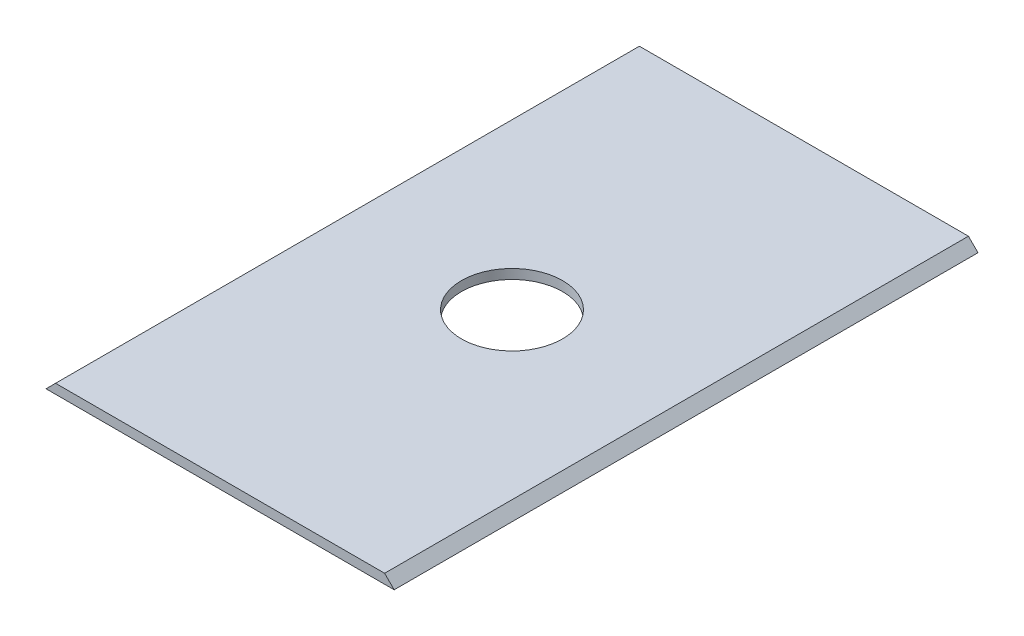
SolidWorks part; units mm, degrees
ref_plane "Front Plane" through (0, 0, 0) normal (0, 0, 1) x (1, 0, 0)
ref_plane "Top Plane" through (0, 0, 0) normal (0, 1, 0) x (1, 0, 0)
ref_plane "Right Plane" through (0, 0, 0) normal (1, 0, 0) x (0, 0, -1)
sketch "Sketch1" plane through (0, 0, 0) normal (0, 0, 1) x (1, 0, 0)
  line L0 (0, 0) -> (65.6, 0)
  line L1 (65.6, 0) -> (63.8, 1.8)
  line L2 (63.8, 1.8) -> (1.8, 1.8)
  line L3 (1.8, 1.8) -> (0, 0)
  dimension "D1" = 1.8
  dimension "D2" = 65.6
  dimension "D3" = 45
extrude "Boss-Extrude1" add sketch "Sketch1" along normal blind 110
sketch "Sketch2" plane through (0, 1.8, 0) normal (0, 1, 0) x (1, 0, 0)
  line L0 (32.8, -110) -> (32.8, 0) construction
  line L1 (63.8, -110) -> (1.8, -110) construction
  line L2 (63.8, 0) -> (1.8, 0) construction
  line L3 (1.8, -55) -> (63.8, -55) construction
  line L4 (1.8, -110) -> (1.8, 0) construction
  line L5 (63.8, -110) -> (63.8, 0) construction
  circle A0 centre (32.8, -55) radius 9.525
  dimension "D1" = 19.05
extrude "Cut-Extrude1" cut sketch "Sketch2" against normal through all
